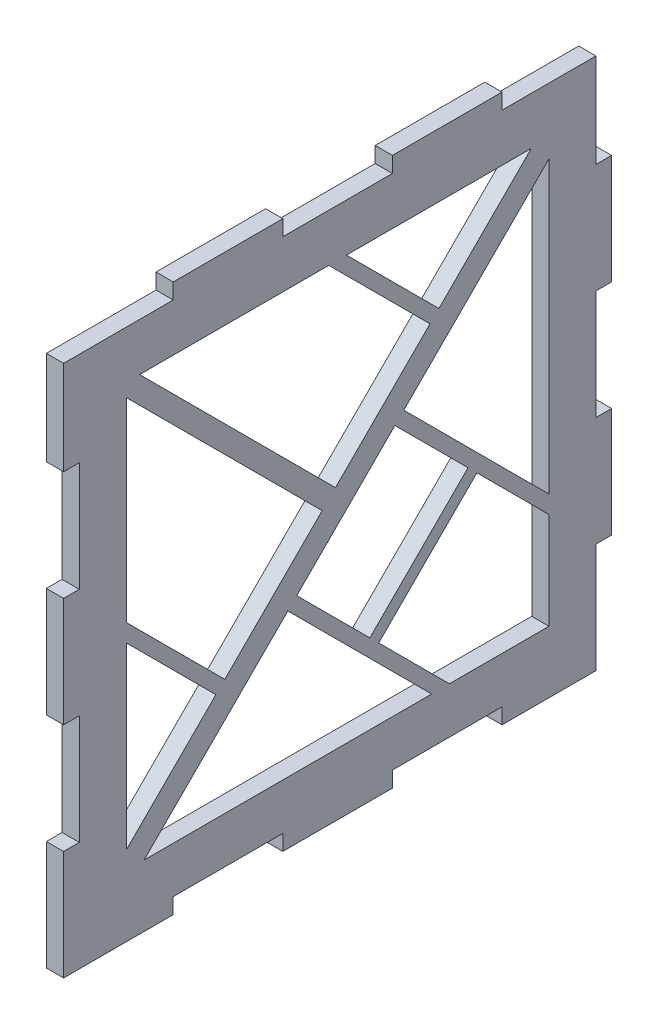
SolidWorks part; units mm, degrees
ref_plane "Спереди" through (0, 0, 0) normal (0, 0, 1) x (1, 0, 0)
ref_plane "Сверху" through (0, 0, 0) normal (0, 1, 0) x (1, 0, 0)
ref_plane "Справа" through (0, 0, 0) normal (1, 0, 0) x (0, 0, -1)
other "Configuration Table"
sketch "Эскиз1" plane through (0, 0, 0) normal (1, 0, 0) x (0, 0, -1)
  line L0 (0.002, 0.0004) -> (175.002, 0.0004)
  line L5 (0.002, 0.0004) -> (0.002, 175.0004)
  line L6 (0.002, 175.0004) -> (175.002, 175.0004)
  line L7 (175, 175.0004) -> (175, 0)
  line L8 (175.002, 0.0004) -> (169.502, 0.0004)
  line L9 (175, 70) -> (175, 35.0004)
  line L13 (0.002, 175.0004) -> (35, 175.0004)
  line L14 (0.002, 175.0004) -> (0.002, 170.0004)
  line L15 (0.002, 175.0004) -> (28.3353, 175.0004)
  line L16 (0.002, 175.0004) -> (0.002, 170.0004)
  line L17 (58.352, 175.0004) -> (86.6853, 175.0004)
  line L18 (116.702, 175.0004) -> (145.0353, 175.0004)
  line L19 (70.002, 175.0004) -> (70.002, 170.0004)
  line L20 (116.702, 0.0004) -> (145.0353, 0.0004)
  line L21 (58.352, 0.0004) -> (86.6853, 0.0004)
  line L22 (0.002, 0.0004) -> (28.3353, 0.0004)
  line L23 (0.002, 0.0004) -> (0.002, 5.0004)
  line L24 (0.002, 175.0004) -> (35, 175.0004)
  line L27 (175.002, 0.0004) -> (169.502, 0.0004)
  line L28 (20.0314, 19.7711) -> (155.002, 154.7417) construction
  line L40 (0.002, 0.0004) -> (5.002, 0.0004)
  line L59 (0.002, 0.0004) -> (0.002, 5.0004)
  line L60 (175.002, 0.0004) -> (175.002, 5.0004)
  line L62 (139.902, 175.0004) -> (139.902, 170.0004)
  line L63 (139.902, 175.0004) -> (175.002, 175.0004)
  line L64 (175.002, 175.0004) -> (175.002, 170.0004)
  line L66 (105.002, 0.0004) -> (105.002, 5.0004)
  line L67 (0.002, 0.0004) -> (34.902, 0.0004)
  line L68 (0.002, 0.0004) -> (0.002, 5.0004)
  line L69 (175.002, 0.0004) -> (140, 0.0004)
  line L70 (97.791, 42.3497) -> (131.9785, 76.5373) construction
  line L71 (175.002, 0.0004) -> (175.002, 5.0004)
  line L73 (140, 0.0004) -> (175.002, 0.0004)
  line L74 (175.002, 0.0004) -> (175.002, 5.0004)
  line L75 (140, 0.0004) -> (140, 5.0004)
  line L76 (105.002, 0.0004) -> (70, 0.0004)
  line L78 (175.002, 0.0004) -> (169.502, 0.0004)
  line L79 (175.002, 0.0004) -> (175.002, 35.1004)
  line L80 (175, 105.0004) -> (175, 70)
  line L81 (175, 175.0004) -> (170, 175.0004)
  line L88 (175.002, 175.0004) -> (170, 175.0004)
  line L89 (0.002, 70.1004) -> (0.002, 104.9004)
  line L90 (0.002, 0.0004) -> (5.002, 0.0004)
  line L91 (0.002, 0.0004) -> (0.002, 34.9004)
  line L92 (0, 70.0004) -> (0, 105)
  line L93 (0, 0.0004) -> (5.002, 0.0004)
  line L94 (0, 0.0004) -> (0, 35)
  line L95 (0.002, 140.1004) -> (0.002, 175.0004)
  line L96 (0, 35) -> (5.002, 35)
  line L97 (0.002, 175.0004) -> (5.002, 175.0004)
  line L99 (0, 70.0004) -> (5.002, 70.0004)
  line L115 (20.0314, 19.7711) -> (155.002, 19.7711)
  line L116 (20.0314, 19.7711) -> (20.0314, 154.7417)
  line L117 (20.0314, 154.7417) -> (155.002, 154.7417)
  line L118 (155.002, 19.7711) -> (155.002, 154.7417)
  line L119 (17.203, 22.5995) -> (152.1736, 157.5701)
  line L120 (22.8598, 16.9427) -> (157.8305, 151.9133)
  line L121 (20.0314, 154.7417) -> (84.6883, 90.0848) construction
  line L122 (22.1527, 156.863) -> (86.8096, 92.2062)
  line L123 (17.9101, 152.6204) -> (82.567, 87.9635)
  line L124 (50.0558, 55.4523) -> (10.1005, 95.4076) construction
  line L127 (118.431, 123.8275) -> (82.567, 159.6915) construction
  line L128 (117.0167, 122.4133) -> (81.1528, 158.2773)
  line L129 (119.8452, 125.2417) -> (83.9812, 161.1057)
  line L132 (48.6416, 54.0381) -> (8.6863, 93.9934)
  line L133 (51.47, 56.8665) -> (11.5147, 96.8218)
  line L134 (96.3767, 43.7639) -> (130.5643, 77.9515)
  line L137 (67.8179, 72.3227) -> (127.764, 12.3767) construction
  line L138 (69.2321, 73.7369) -> (129.1782, 13.7909)
  line L139 (66.4037, 70.9085) -> (126.3498, 10.9624)
  line L142 (102.0055, 106.5103) -> (166.1661, 42.3497) construction
  line L143 (103.4197, 107.9245) -> (167.5803, 43.7639)
  line L144 (100.5913, 105.0961) -> (164.7519, 40.9355)
  line L147 (0.002, 175.0004) -> (0.002, 170.0004)
  line L148 (0.002, 170.0004) -> (35, 170.0004)
  line L149 (99.2052, 40.9355) -> (133.3927, 75.123)
  line L150 (35, 175.0004) -> (35, 170.0004)
  line L151 (70.002, 175.0004) -> (105, 175.0004)
  line L152 (105, 175.0004) -> (105, 170.0004)
  line L153 (70.002, 170.0004) -> (105, 170.0004)
  line L154 (140.002, 175.0004) -> (140.002, 170.0004)
  line L155 (140.002, 175.0004) -> (175, 175.0004)
  line L156 (175, 175.0004) -> (175, 170.0004)
  line L157 (140.002, 170.0004) -> (175, 170.0004)
  line L158 (0.002, 175.0004) -> (70.002, 175.0004) construction
  line L159 (175, 175.0004) -> (175, 140)
  line L160 (175, 140) -> (170, 140)
  line L161 (170, 175.0004) -> (170, 140)
  line L162 (175, 105.0004) -> (170, 105.0004)
  line L163 (170, 105.0004) -> (170, 70)
  line L164 (175, 70) -> (170, 70)
  line L165 (175, 35.0004) -> (175, 0)
  line L166 (175, 35.0004) -> (170, 35.0004)
  line L167 (170, 35.0004) -> (170, 0)
  line L168 (175, 0) -> (170, 0)
  line L170 (70, 0.0004) -> (70, 5.0004)
  line L172 (35.002, 0.0004) -> (35.002, 5.0004)
  line L173 (35.002, 0.0004) -> (0, 0.0004)
  line L174 (0, 0.0004) -> (0, 5.0004)
  line L176 (175.002, 0.0004) -> (105.002, 0.0004) construction
  line L177 (35.002, 5.0004) -> (70, 5.0004)
  line L178 (105.002, 5.0004) -> (140, 5.0004)
  line L182 (0, 105) -> (5.002, 105)
  line L183 (0, 140.0004) -> (0, 175)
  line L184 (0, 140.0004) -> (5.002, 140.0004)
  line L186 (0, 175) -> (5.002, 175)
  line L187 (0, 0.0004) -> (0, 70.0004) construction
  line L188 (5.002, 140.0004) -> (5.002, 105)
  line L189 (5.002, 70.0004) -> (5.002, 35)
  arc A0 (17.203, 22.5995) -> (22.8598, 16.9427) centre (20.0314, 19.7711) ccw
  arc A1 (157.8305, 151.9133) -> (152.1736, 157.5701) centre (155.002, 154.7417) ccw
  arc A2 (22.1527, 156.863) -> (17.9101, 152.6204) centre (20.0314, 154.7417) ccw
  arc A3 (82.567, 87.9635) -> (86.8096, 92.2062) centre (84.6883, 90.0848) ccw
  arc A6 (117.0167, 122.4133) -> (119.8452, 125.2417) centre (118.431, 123.8275) ccw
  arc A7 (83.9812, 161.1057) -> (81.1528, 158.2773) centre (82.567, 159.6915) ccw
  arc A10 (48.6416, 54.0381) -> (51.47, 56.8665) centre (50.0558, 55.4523) ccw
  arc A11 (11.5147, 96.8218) -> (8.6863, 93.9934) centre (10.1005, 95.4076) ccw
  arc A14 (69.2321, 73.7369) -> (66.4037, 70.9085) centre (67.8179, 72.3227) ccw
  arc A15 (126.3498, 10.9624) -> (129.1782, 13.7909) centre (127.764, 12.3767) ccw
  arc A18 (103.4197, 107.9245) -> (100.5913, 105.0961) centre (102.0055, 106.5103) ccw
  arc A19 (164.7519, 40.9355) -> (167.5803, 43.7639) centre (166.1661, 42.3497) ccw
  arc A20 (96.3767, 43.7639) -> (99.2052, 40.9355) centre (97.791, 42.3497) ccw
  arc A21 (133.3927, 75.123) -> (130.5643, 77.9515) centre (131.9785, 76.5373) ccw
  point P42 (87.5167, 87.2564)
  point P58 (52.3599, 122.4133)
  point P72 (30.0782, 75.43)
  point P77 (100.499, 141.7595)
  point P84 (50.0558, 55.4523)
  point P86 (114.8847, 59.4435)
  point P92 (97.791, 42.3497)
  point P99 (134.0858, 74.43)
  dimension "D1" = 3
  dimension "D2" = 3
  dimension "D3" = 3
  dimension "D4" = 70
  dimension "D5" = 3
extrude "Бобышка-Вытянуть5" add sketch "Эскиз1" along normal blind 5.5
